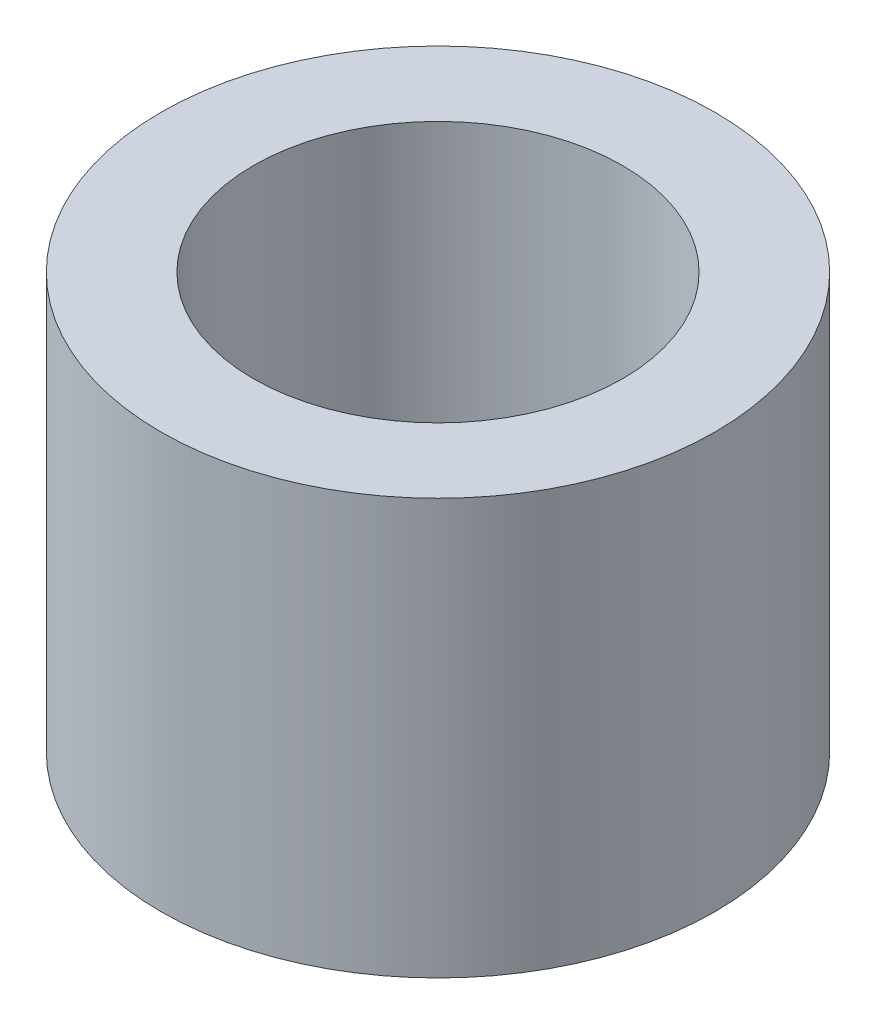
SolidWorks part; units mm, degrees
material "Aluminum Bronze"
ref_plane "Front Plane" through (0, 0, 0) normal (0, 0, 1) x (1, 0, 0)
ref_plane "Top Plane" through (0, 0, 0) normal (0, 1, 0) x (1, 0, 0)
ref_plane "Right Plane" through (0, 0, 0) normal (1, 0, 0) x (0, 0, -1)
sketch "Sketch2" plane through (0, 0, 0) normal (0, 1, 0) x (1, 0, 0)
  circle A0 centre (0, 0) radius 2
  circle A1 centre (0, 0) radius 3
extrude "Boss-Extrude1" add sketch "Sketch2" along normal blind 4.5
